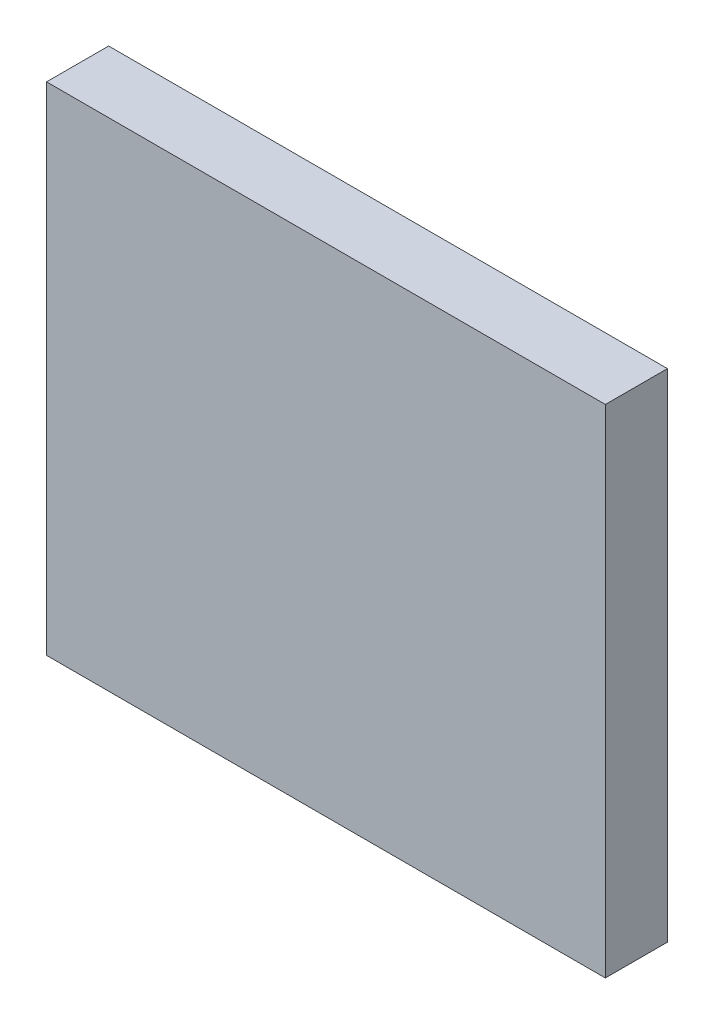
SolidWorks part; units mm, degrees
ref_plane "Plan de face" through (0, 0, 0) normal (0, 0, 1) x (1, 0, 0)
ref_plane "Plan de dessus" through (0, 0, 0) normal (0, 1, 0) x (1, 0, 0)
ref_plane "Plan de droite" through (0, 0, 0) normal (1, 0, 0) x (0, 0, -1)
sketch "Esquisse1" plane through (0, 0, 0) normal (0, 0, 1) x (1, 0, 0)
  line L1 (-135, -120) -> (135, -120)
  line L2 (-135, -120) -> (-135, 120)
  line L3 (-135, 120) -> (135, 120)
  line L4 (135, -120) -> (135, 120)
  line L5 (-135, -120) -> (135, 120) construction
  line L6 (-135, 120) -> (135, -120) construction
  point P1 (0, 0)
  dimension "D1" = 270
  dimension "D2" = 240
extrude "Boss.-Extru.1" add sketch "Esquisse1" along normal blind 30
